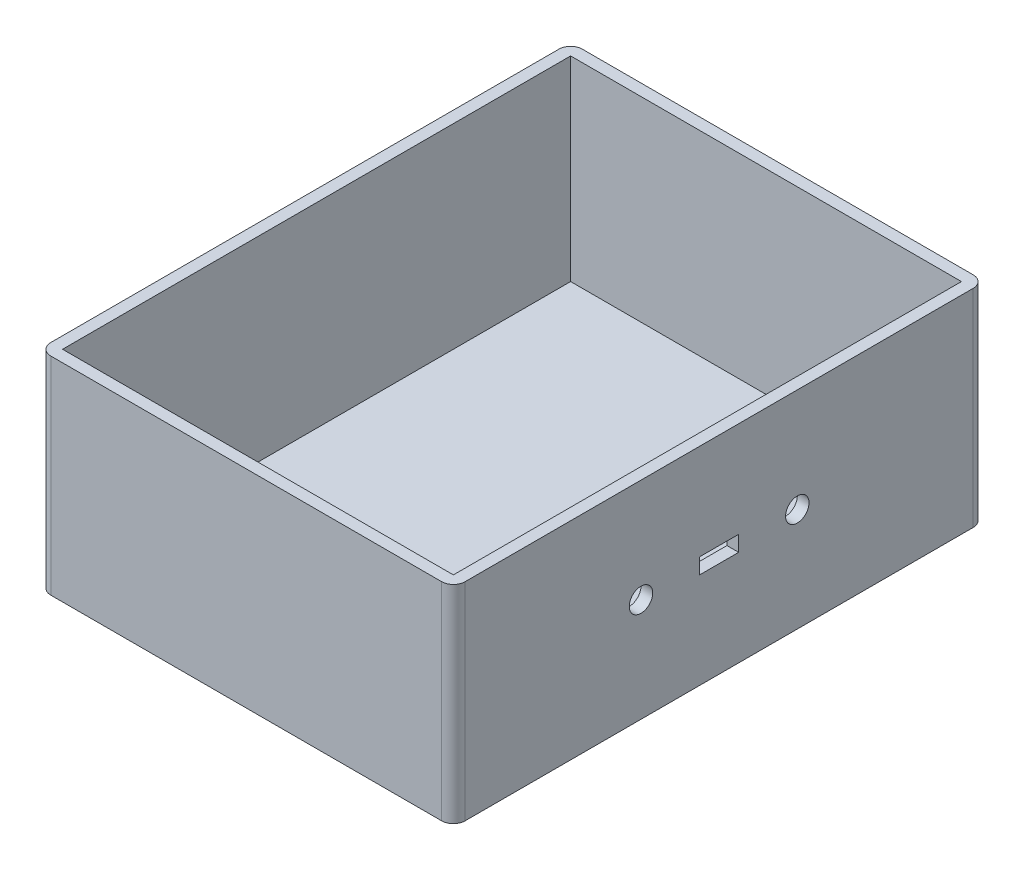
SolidWorks part; units mm, degrees
ref_plane "Plan de face" through (0, 0, 0) normal (0, 0, 1) x (1, 0, 0)
ref_plane "Plan de dessus" through (0, 0, 0) normal (0, 1, 0) x (1, 0, 0)
ref_plane "Plan de droite" through (0, 0, 0) normal (1, 0, 0) x (0, 0, -1)
sketch "Esquisse1" plane through (0, 0, 0) normal (0, 1, 0) x (1, 0, 0)
  line L1 (-53, -68) -> (53, -68)
  line L2 (-53, -68) -> (-53, 68)
  line L3 (-53, 68) -> (53, 68)
  line L4 (53, -68) -> (53, 68)
  line L5 (-53, -68) -> (53, 68) construction
  line L6 (-53, 68) -> (53, -68) construction
  line L7 (-50, 65) -> (50, 65)
  line L8 (-50, 65) -> (-50, -65)
  line L9 (-50, -65) -> (50, -65)
  line L10 (50, 65) -> (50, -65)
  line L11 (-50, 65) -> (50, -65) construction
  line L12 (-50, -65) -> (50, 65) construction
  point P0 (0, 0)
  point P6 (0, 0)
  dimension "D1" = 106
  dimension "D2" = 136
  dimension "D3" = 130
  dimension "D4" = 100
extrude "Boss.-Extru.1" add sketch "Esquisse1" along normal blind 50
sketch "Esquisse2" plane through (0, 0, 0) normal (0, -1, 0) x (1, 0, 0)
  line L1 (53, -68) -> (-53, -68)
  line L2 (53, -68) -> (53, 68)
  line L3 (53, 68) -> (-53, 68)
  line L4 (-53, -68) -> (-53, 68)
extrude "Boss.-Extru.2" add sketch "Esquisse2" along normal blind 3
fillet "Congé1" radius 3 4 edges at (53, 23.5, -68) (-53, 23.5, -68) (-53, 23.5, 68) (53, 23.5, 68)
sketch "Esquisse3" plane through (53, 0, 0) normal (1, 0, 0) x (0, 0, -1)
  line L1 (65, -3) -> (65, 50) construction
  line L13 (-5, 21.5) -> (5, 21.5)
  line L14 (-5, 21.5) -> (-5, 25.5)
  line L15 (-5, 25.5) -> (5, 25.5)
  line L16 (5, 21.5) -> (5, 25.5)
  line L17 (-5, 21.5) -> (5, 25.5) construction
  line L18 (-5, 25.5) -> (5, 21.5) construction
  circle A0 centre (-20, 23.5) radius 3
  circle A1 centre (20, 23.5) radius 3
  dimension "D1" = 10
  dimension "D2" = 4
extrude "Enlèv. mat.-Extru.1" cut sketch "Esquisse3" against normal blind 3
